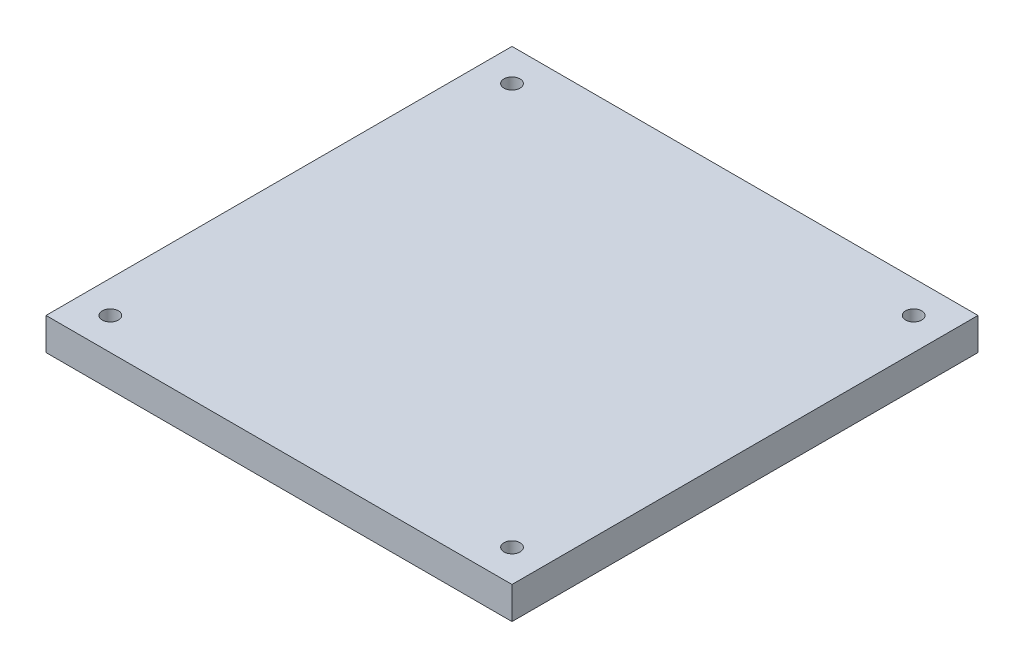
SolidWorks part; units mm, degrees
ref_plane "Front Plane" through (0, 0, 0) normal (0, 0, 1) x (1, 0, 0)
ref_plane "Top Plane" through (0, 0, 0) normal (0, 1, 0) x (1, 0, 0)
ref_plane "Right Plane" through (0, 0, 0) normal (1, 0, 0) x (0, 0, -1)
sketch "Sketch1" plane through (0, 0, 0) normal (0, 1, 0) x (1, 0, 0)
  line L1 (-37.3202, 34.4911) -> (54.6551, 34.4911)
  line L2 (-37.3202, 34.4911) -> (-37.3202, -57.4842)
  line L3 (-37.3202, -57.4842) -> (54.6551, -57.4842)
  line L4 (54.6551, 34.4911) -> (54.6551, -57.4842)
  circle A0 centre (-30.9702, 28.1411) radius 1.5875
  circle A1 centre (48.3051, 28.1411) radius 1.5875
  circle A2 centre (-30.9702, -51.1342) radius 1.5875
  circle A3 centre (48.3051, -51.1342) radius 1.5875
  point P5 (0, 0)
  point P7 (58.2067, -51.1342)
  point P11 (-42.3256, -51.1342)
  point P16 (-31.6895, 42.9595)
  point P17 (0, 0)
  point P18 (0, 0)
  point P19 (54.0543, 38.6614)
extrude "Boss-Extrude1" add sketch "Sketch1" along normal blind 6.35
